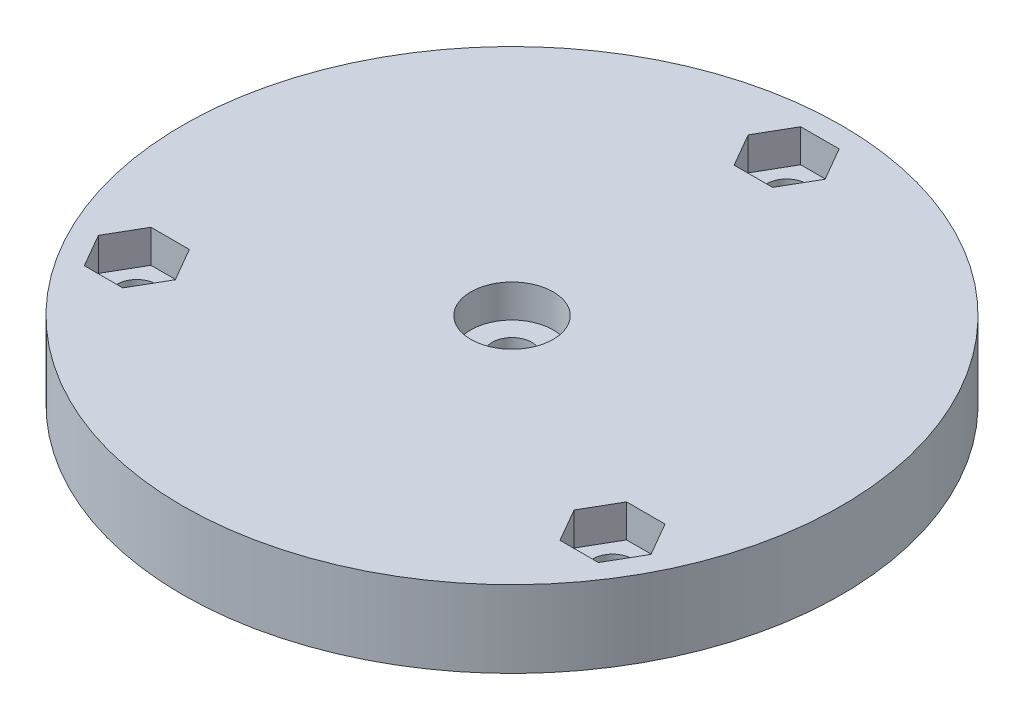
SolidWorks part; units mm, degrees
ref_plane "Front Plane" through (0, 0, 0) normal (0, 0, 1) x (1, 0, 0)
ref_plane "Top Plane" through (0, 0, 0) normal (0, 1, 0) x (1, 0, 0)
ref_plane "Right Plane" through (0, 0, 0) normal (1, 0, 0) x (0, 0, -1)
sketch "Sketch1" plane through (0, 0, 0) normal (0, 1, 0) x (1, 0, 0)
  circle A0 centre (0, 0) radius 30
  circle A1 centre (0, 0) radius 1.8
  circle A2 centre (0, 25) radius 1.8
  circle A3 centre (21.6506, -12.5) radius 1.8
  circle A4 centre (-21.6506, -12.5) radius 1.8
  point P12 (0, 0)
  dimension "D1" = 60
  dimension "D2" = 3.6
  dimension "D3" = 3.6
  dimension "D4" = 25
  dimension "D5" = 3
extrude "Boss-Extrude1" add sketch "Sketch1" along normal blind 7
sketch "Sketch2" plane through (0, 7, 0) normal (0, 1, 0) x (1, 0, 0)
  line L0 (19.9006, -15.5311) -> (23.4006, -15.5311)
  line L1 (3.5, 25) -> (1.75, 28.0311)
  line L2 (1.75, 28.0311) -> (-1.75, 28.0311)
  line L3 (-1.75, 28.0311) -> (-3.5, 25)
  line L4 (-3.5, 25) -> (-1.75, 21.9689)
  line L5 (-1.75, 21.9689) -> (1.75, 21.9689)
  line L6 (1.75, 21.9689) -> (3.5, 25)
  line L7 (23.4006, -15.5311) -> (25.1506, -12.5)
  line L8 (25.1506, -12.5) -> (23.4006, -9.4689)
  line L9 (23.4006, -9.4689) -> (19.9006, -9.4689)
  line L10 (19.9006, -9.4689) -> (18.1506, -12.5)
  line L11 (18.1506, -12.5) -> (19.9006, -15.5311)
  line L12 (-23.4006, -9.4689) -> (-25.1506, -12.5)
  line L13 (-25.1506, -12.5) -> (-23.4006, -15.5311)
  line L14 (-23.4006, -15.5311) -> (-19.9006, -15.5311)
  line L15 (-19.9006, -15.5311) -> (-18.1506, -12.5)
  line L16 (-18.1506, -12.5) -> (-19.9006, -9.4689)
  line L17 (-19.9006, -9.4689) -> (-23.4006, -9.4689)
  circle A0 centre (0, 0) radius 3.75
  circle A1 centre (0, 25) radius 3.0311 construction
  circle A2 centre (21.6506, -12.5) radius 3.0311 construction
  circle A3 centre (-21.6506, -12.5) radius 3.0311 construction
  point P31 (0, 0)
  dimension "D1" = 7.5
  dimension "D2" = 3.5
  dimension "D3" = 3
extrude "Cut-Extrude1" cut sketch "Sketch2" against normal blind 3
